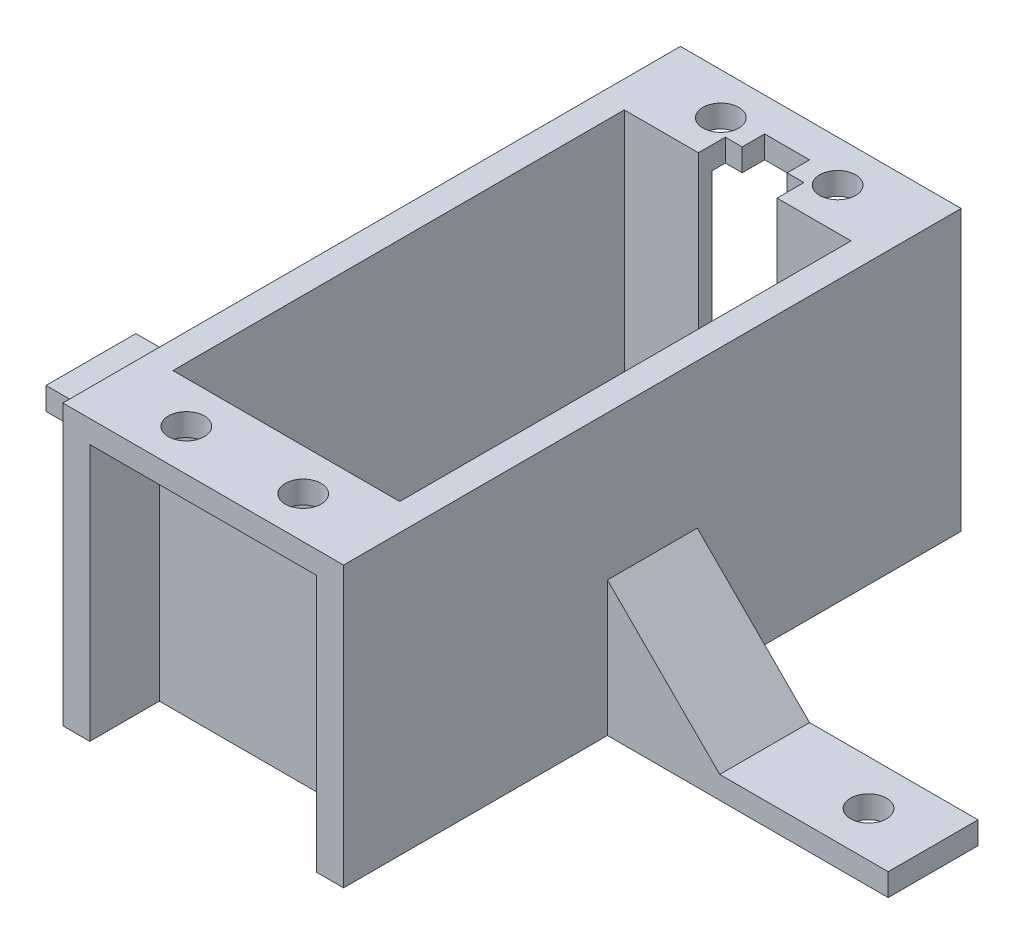
SolidWorks part; units mm, degrees
ref_plane "Front Plane" through (0, 0, 0) normal (0, 0, 1) x (1, 0, 0)
ref_plane "Top Plane" through (0, 0, 0) normal (0, 1, 0) x (1, 0, 0)
ref_plane "Right Plane" through (0, 0, 0) normal (1, 0, 0) x (0, 0, -1)
sketch "Sketch2" plane through (0, 0, 0) normal (0, 1, 0) x (1, 0, 0)
  line L1 (-37.5, 4) -> (37.5, 4)
  line L2 (-37.5, 4) -> (-37.5, -4)
  line L3 (-37.5, -4) -> (37.5, -4)
  line L4 (37.5, 4) -> (37.5, -4)
  line L5 (-37.5, 4) -> (37.5, -4) construction
  line L6 (-37.5, -4) -> (37.5, 4) construction
  circle A1 centre (-31.75, 0) radius 1.6
  circle A2 centre (31.75, 0) radius 1.6
  point P0 (0, 0)
extrude "Boss-Extrude1" add sketch "Sketch2" along normal blind 2
sketch "Sketch3" plane through (0, 2, 0) normal (0, 1, 0) x (1, 0, 0)
  line L1 (-12.5, -22.5) -> (12.5, -22.5)
  line L2 (-12.5, -22.5) -> (-12.5, -4)
  line L3 (-37.5, -4) -> (37.5, -4) construction
  line L4 (-12.5, -4) -> (12.5, -4)
  line L5 (12.5, -4) -> (12.5, -22.5)
  point P0 (0, -4)
  point P6 (0, -22.5)
extrude "Boss-Extrude2" add sketch "Sketch3" against normal up to surface (2 mm away) up to face at (0, 0, 0)
sketch "Sketch4" plane through (0, 0, -4) normal (0, 0, -1) x (-1, 0, 0)
  line L4 (-12.5, 0) -> (12.5, 0)
  line L5 (-12.5, 2) -> (-12.5, 0)
  line L6 (12.5, 2) -> (-12.5, 2)
  line L7 (12.5, 0) -> (12.5, 2)
  line L8 (-12.5, 0) -> (12.5, 0)
  line L9 (-12.5, 2) -> (-12.5, 0)
  line L10 (12.5, 2) -> (-12.5, 2)
  line L11 (12.5, 0) -> (12.5, 2)
  dimension "D1" = 0
extrude "Boss-Extrude3" add sketch "Sketch4" along normal blind 18.5
sketch "Sketch5" plane through (0, 2, 0) normal (0, 1, 0) x (1, 0, 0)
  line L1 (-5.1, 20.1) -> (5.1, 20.1)
  line L2 (-5.1, 20.1) -> (-5.1, -20.1)
  line L3 (-5.1, -20.1) -> (5.1, -20.1)
  line L4 (5.1, 20.1) -> (5.1, -20.1)
  line L5 (-5.1, 20.1) -> (5.1, -20.1) construction
  line L6 (-5.1, -20.1) -> (5.1, 20.1) construction
  point P0 (0, 0)
extrude "Cut-Extrude1" cut sketch "Sketch5" against normal blind 18.5
sketch "Sketch6" plane through (0, 2, 0) normal (0, 1, 0) x (1, 0, 0)
  line L0 (-12.5, 4) -> (-12.5, -4)
  line L1 (12.5, 4) -> (12.5, -4)
  line L3 (-5.1, 20.1) -> (5.1, 20.1)
  line L4 (-5.1, 20.1) -> (-5.1, -20.1)
  line L5 (-5.1, -20.1) -> (5.1, -20.1)
  line L6 (5.1, 20.1) -> (5.1, -20.1)
  line L12 (37.5, -4) -> (37.5, 4)
  line L13 (37.5, 4) -> (12.5, 4)
  line L14 (12.5, 4) -> (12.5, 22.5)
  line L15 (12.5, 22.5) -> (-12.5, 22.5)
  line L16 (-12.5, 22.5) -> (-12.5, 4)
  line L17 (-12.5, 4) -> (-37.5, 4)
  line L18 (-37.5, 4) -> (-37.5, -4)
  line L19 (-37.5, -4) -> (-12.5, -4)
  line L20 (-12.5, -4) -> (-12.5, -22.5)
  line L21 (-12.5, -22.5) -> (12.5, -22.5)
  line L22 (12.5, -22.5) -> (12.5, -4)
  line L23 (12.5, -4) -> (37.5, -4)
  line L26 (12.5, 4) -> (12.5, 22.5)
  line L27 (12.5, 22.5) -> (-12.5, 22.5)
  line L28 (-12.5, 22.5) -> (-12.5, 4)
  line L32 (-12.5, -4) -> (-12.5, -22.5)
  line L33 (-12.5, -22.5) -> (12.5, -22.5)
  line L34 (12.5, -22.5) -> (12.5, -4)
  dimension "D1" = 0
extrude "Boss-Extrude4" add sketch "Sketch6" along normal blind 24.9
sketch "Sketch8" plane through (0, 26.9, 0) normal (0, 1, 0) x (1, 0, 0)
  line L1 (-12.5, 22.5) -> (12.5, 22.5)
  line L2 (-12.5, 22.5) -> (-12.5, 29.5)
  line L3 (-12.5, 29.5) -> (12.5, 29.5)
  line L4 (12.5, 22.5) -> (12.5, 29.5)
  line L5 (-12.5, -22.5) -> (12.5, -22.5)
  line L6 (-12.5, -22.5) -> (-12.5, -29.5)
  line L7 (-12.5, -29.5) -> (12.5, -29.5)
  line L8 (12.5, -22.5) -> (12.5, -29.5)
extrude "Boss-Extrude5" add sketch "Sketch8" against normal blind 2
sketch "Sketch9" plane through (0, 24.9, 0) normal (0, -1, 0) x (1, 0, 0)
  circle A1 centre (5.2, 23.8) radius 1.6
  circle A2 centre (-5.2, 23.8) radius 1.6
  circle A3 centre (-5.2, -23.8) radius 1.6
  circle A4 centre (5.2, -23.8) radius 1.6
extrude "Cut-Extrude2" cut sketch "Sketch9" against normal blind 2
sketch "Sketch10" plane through (0, 0, 0) normal (0, -1, 0) x (1, 0, 0)
  line L1 (-10.1, 20.1) -> (10.1, 20.1)
  line L2 (-10.1, 20.1) -> (-10.1, -20.1)
  line L3 (-10.1, -20.1) -> (10.1, -20.1)
  line L4 (10.1, 20.1) -> (10.1, -20.1)
  line L5 (-10.1, 20.1) -> (10.1, -20.1) construction
  line L6 (-10.1, -20.1) -> (10.1, 20.1) construction
  point P0 (0, 0)
extrude "Cut-Extrude3" cut sketch "Sketch10" against normal blind 77
sketch "Sketch11" plane through (0, 0, 0) normal (0, -1, 0) x (1, 0, 0)
  line L1 (3.5, -20.1) -> (3.5, -22.5)
  line L2 (12.5, -22.5) -> (-12.5, -22.5) construction
  line L3 (3.5, -22.5) -> (-3.5, -22.5)
  line L4 (-3.5, -22.5) -> (-3.5, -20.1)
  line L5 (-3.5, -20.1) -> (3.5, -20.1)
extrude "Cut-Extrude4" cut sketch "Sketch11" against normal blind 77
sketch "Sketch12" plane through (0, 0, 0) normal (0, -1, 0) x (1, 0, 0)
  line L0 (-12.5, 22.5) -> (-12.5, 29.5)
  line L1 (-12.5, 29.5) -> (-10.1, 29.5)
  line L2 (-12.5, 29.5) -> (12.5, 29.5) construction
  line L3 (-10.1, 29.5) -> (-10.1, 22.5)
  line L4 (12.5, 22.5) -> (6.1327, 22.5) construction
  line L5 (-10.1, 22.5) -> (-12.5, 22.5)
  line L6 (-12.5, -22.5) -> (-6.1327, -22.5) construction
  line L7 (-10.1, -22.5) -> (-12.5, -22.5)
  line L8 (-10.1, -22.5) -> (-10.1, -29.5)
  line L9 (-10.1, -29.5) -> (-12.5, -29.5)
  line L10 (-12.5, -22.5) -> (-12.5, -29.5)
  line L11 (12.5, 22.5) -> (-12.5, 22.5) construction
  line L12 (12.5, 29.5) -> (10.1, 29.5)
  line L13 (12.5, 29.5) -> (12.5, 22.5)
  line L14 (12.5, 22.5) -> (10.1, 22.5)
  line L15 (10.1, 29.5) -> (10.1, 22.5)
  line L16 (3.5, -22.5) -> (4.2673, -22.5) construction
  line L17 (10.1, -22.5) -> (12.5, -22.5)
  line L18 (10.1, -22.5) -> (10.1, -29.5)
  line L19 (10.1, -29.5) -> (12.5, -29.5)
  line L20 (12.5, -22.5) -> (12.5, -29.5)
extrude "Boss-Extrude6" add sketch "Sketch12" against normal up to surface (24.9 mm away) up to face at (0, 24.9, 24.975)
sketch "Sketch13" plane through (0, 26.9, 0) normal (0, 1, 0) x (1, 0, 0)
  line L0 (3.5, 22.5) -> (-3.5, 22.5) construction
  line L1 (-2, 24.5) -> (2, 24.5)
  line L2 (-2, 24.5) -> (-2, 20.5)
  line L3 (-2, 20.5) -> (2, 20.5)
  line L4 (2, 24.5) -> (2, 20.5)
  line L5 (-2, 24.5) -> (2, 20.5) construction
  line L6 (-2, 20.5) -> (2, 24.5) construction
  point P0 (0, 22.5)
extrude "Cut-Extrude5" cut sketch "Sketch13" against normal blind 77
sketch "Sketch14" plane through (0, 2, 0) normal (0, 1, 0) x (1, 0, 0)
  line L4 (-12.5, -4) -> (-12.5, 4)
  line L5 (-12.5, 4) -> (-37.5, 4)
  line L6 (-37.5, 4) -> (-37.5, -4)
  line L7 (-37.5, -4) -> (-12.5, -4)
  line L8 (-12.5, -4) -> (-12.5, 4)
  line L9 (-12.5, 4) -> (-37.5, 4)
  line L10 (-37.5, 4) -> (-37.5, -4)
  line L11 (-37.5, -4) -> (-12.5, -4)
  line L12 (12.5, 4) -> (12.5, -4)
  line L13 (12.5, -4) -> (37.5, -4)
  line L14 (37.5, -4) -> (37.5, 4)
  line L15 (37.5, 4) -> (12.5, 4)
  line L16 (12.5, 4) -> (12.5, -4)
  line L17 (12.5, -4) -> (37.5, -4)
  line L18 (37.5, -4) -> (37.5, 4)
  line L19 (37.5, 4) -> (12.5, 4)
  circle A0 centre (-31.75, 0) radius 1.6 construction
  circle A1 centre (-31.75, 0) radius 1.6
  circle A2 centre (31.75, 0) radius 1.6 construction
  circle A3 centre (31.75, 0) radius 1.6
  dimension "D1" = 0
  dimension "D2" = 0
extrude "Boss-Extrude7" add sketch "Sketch14" along normal blind 2
sketch "Sketch15" plane through (0, 0, 0) normal (0, -1, 0) x (1, 0, 0)
  line L28 (10.1, -20.1) -> (3.5, -20.1)
  line L29 (3.5, -20.1) -> (3.5, -22.5)
  line L30 (3.5, -22.5) -> (10.1, -22.5)
  line L31 (10.1, -22.5) -> (10.1, -29.5)
  line L32 (10.1, -29.5) -> (12.5, -29.5)
  line L33 (12.5, -29.5) -> (12.5, -4)
  line L34 (12.5, -4) -> (37.5, -4)
  line L35 (37.5, -4) -> (37.5, 4)
  line L36 (37.5, 4) -> (12.5, 4)
  line L37 (12.5, 4) -> (12.5, 29.5)
  line L38 (12.5, 29.5) -> (10.1, 29.5)
  line L39 (10.1, 29.5) -> (10.1, 22.5)
  line L40 (10.1, 22.5) -> (-10.1, 22.5)
  line L41 (-10.1, 22.5) -> (-10.1, 29.5)
  line L42 (-10.1, 29.5) -> (-12.5, 29.5)
  line L43 (-12.5, 29.5) -> (-12.5, 4)
  line L44 (-12.5, 4) -> (-37.5, 4)
  line L45 (-37.5, 4) -> (-37.5, -4)
  line L46 (-37.5, -4) -> (-12.5, -4)
  line L47 (-12.5, -4) -> (-12.5, -29.5)
  line L48 (-12.5, -29.5) -> (-10.1, -29.5)
  line L49 (-10.1, -29.5) -> (-10.1, -22.5)
  line L50 (-10.1, -22.5) -> (-3.5, -22.5)
  line L51 (-3.5, -22.5) -> (-3.5, -20.1)
  line L52 (-3.5, -20.1) -> (-10.1, -20.1)
  line L53 (-10.1, -20.1) -> (-10.1, 20.1)
  line L54 (-10.1, 20.1) -> (10.1, 20.1)
  line L55 (10.1, 20.1) -> (10.1, -20.1)
  line L56 (10.1, -20.1) -> (3.5, -20.1)
  line L57 (3.5, -20.1) -> (3.5, -22.5)
  line L58 (3.5, -22.5) -> (10.1, -22.5)
  line L59 (10.1, -22.5) -> (10.1, -29.5)
  line L60 (10.1, -29.5) -> (12.5, -29.5)
  line L61 (12.5, -29.5) -> (12.5, -4)
  line L62 (12.5, -4) -> (37.5, -4)
  line L63 (37.5, -4) -> (37.5, 4)
  line L64 (37.5, 4) -> (12.5, 4)
  line L65 (12.5, 4) -> (12.5, 29.5)
  line L66 (12.5, 29.5) -> (10.1, 29.5)
  line L67 (10.1, 29.5) -> (10.1, 22.5)
  line L68 (10.1, 22.5) -> (-10.1, 22.5)
  line L69 (-10.1, 22.5) -> (-10.1, 29.5)
  line L70 (-10.1, 29.5) -> (-12.5, 29.5)
  line L71 (-12.5, 29.5) -> (-12.5, 4)
  line L72 (-12.5, 4) -> (-37.5, 4)
  line L73 (-37.5, 4) -> (-37.5, -4)
  line L74 (-37.5, -4) -> (-12.5, -4)
  line L75 (-12.5, -4) -> (-12.5, -29.5)
  line L76 (-12.5, -29.5) -> (-10.1, -29.5)
  line L77 (-10.1, -29.5) -> (-10.1, -22.5)
  line L78 (-10.1, -22.5) -> (-3.5, -22.5)
  line L79 (-3.5, -22.5) -> (-3.5, -20.1)
  line L80 (-3.5, -20.1) -> (-10.1, -20.1)
  line L81 (-10.1, -20.1) -> (-10.1, 20.1)
  line L82 (-10.1, 20.1) -> (10.1, 20.1)
  line L83 (10.1, 20.1) -> (10.1, -20.1)
  dimension "D1" = 0
extrude "Cut-Extrude6" cut sketch "Sketch15" against normal blind 2
chamfer "Chamfer1" distance 10 angle 45 2 edges at (12.5, 4, 0) (-12.5, 4, 0)
sketch "Sketch16" plane through (0, 0, 22.5) normal (0, 0, 1) x (1, 0, 0)
  line L8 (-10.1, 2) -> (10.1, 2)
  line L9 (10.1, 2) -> (10.1, 24.9)
  line L10 (10.1, 24.9) -> (6.1327, 24.9)
  line L11 (6.1327, 24.9) -> (4.2673, 24.9)
  line L12 (4.2673, 24.9) -> (-4.2673, 24.9)
  line L13 (-4.2673, 24.9) -> (-6.1327, 24.9)
  line L14 (-6.1327, 24.9) -> (-10.1, 24.9)
  line L15 (-10.1, 24.9) -> (-10.1, 2)
  line L16 (-10.1, 2) -> (10.1, 2)
  line L17 (10.1, 2) -> (10.1, 24.9)
  line L18 (10.1, 24.9) -> (6.1327, 24.9)
  line L19 (6.1327, 24.9) -> (4.2673, 24.9)
  line L20 (4.2673, 24.9) -> (-4.2673, 24.9)
  line L21 (-4.2673, 24.9) -> (-6.1327, 24.9)
  line L22 (-6.1327, 24.9) -> (-10.1, 24.9)
  line L23 (-10.1, 24.9) -> (-10.1, 2)
  dimension "D1" = 0
extrude "Cut-Extrude7" cut sketch "Sketch16" against normal blind 1.2
sketch "Sketch17" plane through (0, 0, -22.5) normal (0, 0, -1) x (-1, 0, 0)
  line L12 (10.1, 2) -> (10.1, 24.9)
  line L13 (-10.1, 2) -> (10.1, 2)
  line L14 (-10.1, 24.9) -> (-10.1, 2)
  line L15 (10.1, 24.9) -> (-10.1, 24.9)
  line L16 (10.1, 2) -> (10.1, 24.9)
  line L17 (-10.1, 2) -> (10.1, 2)
  line L18 (-10.1, 24.9) -> (-10.1, 2)
  line L19 (10.1, 24.9) -> (-10.1, 24.9)
  dimension "D1" = 0
extrude "Cut-Extrude8" cut sketch "Sketch17" against normal blind 1.2
sketch "Sketch18" plane through (0, 0, -29.5) normal (0, 0, -1) x (-1, 0, 0)
  line L8 (10.1, 2) -> (12.5, 2)
  line L9 (12.5, 2) -> (12.5, 26.9)
  line L10 (12.5, 26.9) -> (-12.5, 26.9)
  line L11 (-12.5, 26.9) -> (-12.5, 2)
  line L12 (-12.5, 2) -> (-10.1, 2)
  line L13 (-10.1, 2) -> (-10.1, 24.9)
  line L14 (-10.1, 24.9) -> (10.1, 24.9)
  line L15 (10.1, 24.9) -> (10.1, 2)
  line L16 (10.1, 2) -> (12.5, 2)
  line L17 (12.5, 2) -> (12.5, 26.9)
  line L18 (12.5, 26.9) -> (-12.5, 26.9)
  line L19 (-12.5, 26.9) -> (-12.5, 2)
  line L20 (-12.5, 2) -> (-10.1, 2)
  line L21 (-10.1, 2) -> (-10.1, 24.9)
  line L22 (-10.1, 24.9) -> (10.1, 24.9)
  line L23 (10.1, 24.9) -> (10.1, 2)
  dimension "D1" = 0
extrude "Cut-Extrude9" cut sketch "Sketch18" against normal blind 2
sketch "Sketch19" plane through (0, 0, 29.5) normal (0, 0, 1) x (1, 0, 0)
  line L8 (10.1, 2) -> (12.5, 2)
  line L9 (12.5, 2) -> (12.5, 26.9)
  line L10 (12.5, 26.9) -> (-12.5, 26.9)
  line L11 (-12.5, 26.9) -> (-12.5, 2)
  line L12 (-12.5, 2) -> (-10.1, 2)
  line L13 (-10.1, 2) -> (-10.1, 24.9)
  line L14 (-10.1, 24.9) -> (10.1, 24.9)
  line L15 (10.1, 24.9) -> (10.1, 2)
  line L16 (10.1, 2) -> (12.5, 2)
  line L17 (12.5, 2) -> (12.5, 26.9)
  line L18 (12.5, 26.9) -> (-12.5, 26.9)
  line L19 (-12.5, 26.9) -> (-12.5, 2)
  line L20 (-12.5, 2) -> (-10.1, 2)
  line L21 (-10.1, 2) -> (-10.1, 24.9)
  line L22 (-10.1, 24.9) -> (10.1, 24.9)
  line L23 (10.1, 24.9) -> (10.1, 2)
  dimension "D1" = 0
extrude "Cut-Extrude10" cut sketch "Sketch19" against normal blind 2
